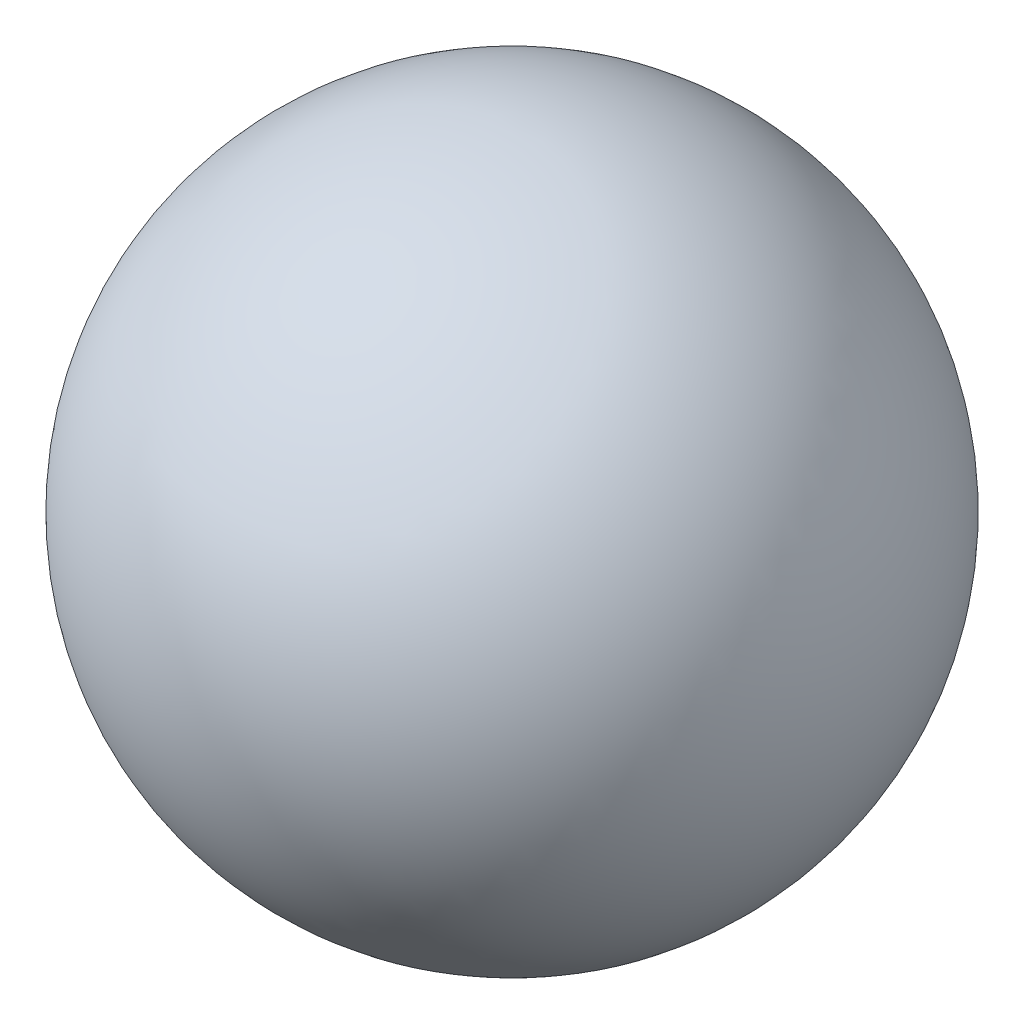
SolidWorks part; units mm, degrees
material "Stainless Steel (ferritic)"
ref_plane "Front Plane" through (0, 0, 0) normal (0, 0, 1) x (1, 0, 0)
ref_plane "Top Plane" through (0, 0, 0) normal (0, 1, 0) x (1, 0, 0)
ref_plane "Right Plane" through (0, 0, 0) normal (1, 0, 0) x (0, 0, -1)
sketch "Sketch1" plane through (0, 0, 0) normal (0, 0, 1) x (1, 0, 0)
  line L0 (0, 900) -> (0, -900)
  arc A0 (0, -900) -> (0, 900) centre (0, 0) ccw
  dimension "D1" = 1800
revolve "Revolve-Thin8" add sketch "Sketch1" angle 360 about L0 wall 10
